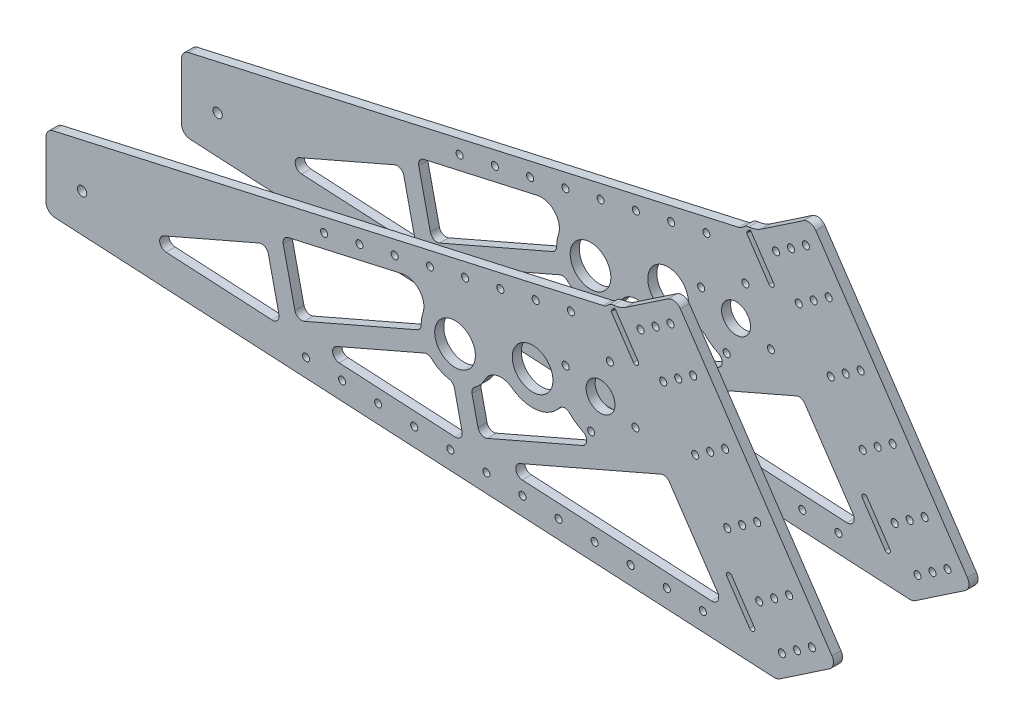
SolidWorks part; units mm, degrees
other "Markup1"
sketch "Sketch2"
sketch "Sketch9" plane through (0, 0, 0) normal (0, 0, 1) x (1, 0, 0)
sketch "Sketch12" plane through (116.0373, 167.646, 63.5) normal (0, 0, 1) x (1, 0, 0)
sketch "Sketch13" plane through (116.0373, 167.646, 63.5) normal (0, 0, 1) x (1, 0, 0)
sketch "Sketch14" plane through (116.0373, 167.646, 63.5) normal (0, 0, 1) x (1, 0, 0)
sketch "Sketch16" plane through (116.0373, 167.646, 63.5) normal (0, 0, 1) x (1, 0, 0)
sketch "Sketch17" plane through (116.0373, 167.8557, 63.5) normal (0, 0, 1) x (1, 0, 0)
sketch "Sketch18" plane through (116.0373, 167.7906, 57.15) normal (0, 0, 1) x (1, 0, 0)
sketch "Sketch19" plane through (84.5137, 127.089, 57.15) normal (0, 0, 1) x (1, 0, 0)
sketch "Sketch21" plane through (128.7373, 167.7931, 57.15) normal (0, 0, 1) x (1, 0, 0)
sketch "Sketch22" plane through (128.7373, 167.7931, 57.15) normal (0, 0, 1) x (1, 0, 0)
sketch "Sketch23" plane through (128.7373, 167.7931, 57.15) normal (0, 0, 1) x (1, 0, 0)
material "6061-T6 (SS)"
ref_plane "Front Plane" through (0, 0, 0) normal (0, 0, 1) x (1, 0, 0)
ref_plane "Top Plane" through (0, 0, 0) normal (0, 1, 0) x (1, 0, 0)
ref_plane "Right Plane" through (0, 0, 0) normal (1, 0, 0) x (0, 0, -1)
sketch "Grid" plane through (0, 0, 0) normal (0, 0, 1) x (1, 0, 0)
  line L0 (-23.2766, 0) -> (153.3593, 0) construction
  line L1 (0, 0) -> (0, 151.4205) construction
  line L6 (-1009.65, 1168.4) -> (-1009.65, 0) construction
  line L15 (-361.95, 520.7) -> (-803.275, 520.7)
  line L16 (-361.95, 520.7) -> (-361.95, 0)
  line L17 (-361.95, 0) -> (-803.275, 0)
  line L18 (-803.275, 520.7) -> (-803.275, 0)
  line L19 (-803.275, 0) -> (-1244.6, 0)
  line L20 (-803.275, 0) -> (-803.275, 825.5)
  line L21 (-803.275, 825.5) -> (-1244.6, 825.5)
  line L22 (-1244.6, 0) -> (-1244.6, 825.5)
  line L23 (-1030.732, 0) -> (-988.568, 0)
  line L24 (-1030.732, 0) -> (-1030.732, 1168.4)
  line L25 (-1030.732, 1168.4) -> (-988.568, 1168.4)
  line L26 (-988.568, 0) -> (-988.568, 1168.4)
  line L27 (-598.932, 0) -> (-556.768, 0)
  line L28 (-598.932, 0) -> (-598.932, 863.6)
  line L29 (-598.932, 863.6) -> (-556.768, 863.6)
  line L30 (-556.768, 0) -> (-556.768, 863.6)
  line L31 (-577.85, 863.6) -> (-577.85, 0) construction
  line L32 (-361.95, 520.7) -> (-361.95, 596.9) construction
  line L33 (-803.275, 825.5) -> (-803.275, 901.7) construction
  line L34 (-370.0766, 0) -> (-263.7141, 304.8)
  line L35 (-263.7141, 304.8) -> (-157.3516, 0)
  line L36 (-157.3516, 0) -> (-370.0766, 0)
  circle A0 centre (-100.3958, 159.9664) radius 120.65
  dimension "D3" = 241.3
  dimension "D2" = 76.2
  dimension "D4" = 304.8
  dimension "D5" = 212.725
  dimension "D7" = 42.164
  dimension "D8" = 520.7
  dimension "D9" = 304.8
  dimension "D10" = 1168.4
  dimension "D11" = 863.6
  dimension "D12" = 361.95
  dimension "D13" = 577.85
  dimension "D14" = 803.275
  dimension "D15" = 1009.65
sketch "ChassisXY" plane through (0, 0, 0) normal (0, 0, 1) x (1, 0, 0)
  line L0 (755.65, 93.726) -> (95.25, 93.726)
  line L1 (755.65, 93.726) -> (755.65, 42.926)
  line L2 (755.65, 42.926) -> (95.25, 42.926)
  line L3 (95.25, 93.726) -> (95.25, 42.926)
  line L15 (736.7108, 119.126) -> (675.4349, 119.126)
  line L16 (787.4, 42.926) -> (768.35, 42.926)
  line L19 (63.5, 169.926) -> (82.55, 169.926)
  line L20 (736.7108, 119.126) -> (694.5957, 90.719) construction
  line L21 (736.7108, 119.126) -> (717.55, 147.533) construction
  line L22 (694.5957, 90.719) -> (675.4349, 119.126) construction
  line L23 (717.55, 147.533) -> (675.4349, 119.126) construction
  line L27 (63.5, 169.926) -> (63.5, 42.926)
  line L31 (88.9, 42.926) -> (88.9, 1979.9925) construction
  line L32 (62.806, 1979.9925) -> (762, 1979.9925) construction
  line L33 (63.5, 42.926) -> (82.55, 42.926)
  line L36 (88.9, 1320.8) -> (762, 1320.8) construction
  line L37 (88.9, 988.6997) -> (131.0151, 1017.1067) construction
  line L45 (63.5, 42.926) -> (31.75, 42.926)
  line L46 (717.55, 147.533) -> (675.4349, 119.126) construction
  line L47 (717.55, 147.533) -> (-518.4596, 1979.9925) construction
  line L48 (675.4349, 119.126) -> (-560.5747, 1951.5855) construction
  line L49 (-518.4596, 1979.9925) -> (-560.5747, 1951.5855) construction
  line L50 (63.5, 42.926) -> (63.5, 169.926)
  line L51 (0, 74.676) -> (0, 138.176)
  line L52 (31.75, 169.926) -> (63.5, 169.926)
  line L54 (425.45, 93.726) -> (425.45, 42.926) construction
  line L55 (762, 42.926) -> (762, 1979.9925) construction
  line L56 (819.15, 169.926) -> (787.4, 169.926)
  line L57 (850.9, 74.676) -> (850.9, 138.176)
  line L58 (787.4, 42.926) -> (787.4, 169.926)
  line L59 (787.4, 42.926) -> (819.15, 42.926)
  line L60 (82.55, 169.926) -> (82.55, 42.926)
  line L61 (768.35, 169.926) -> (768.35, 42.926)
  line L62 (787.4, 169.926) -> (768.35, 169.926)
  line L63 (787.4, 169.926) -> (787.4, 42.926)
  line L64 (0, 0) -> (0, 200151.4205) construction
  line L65 (-200023.2766, 0) -> (200153.3593, 0) construction
  line L66 (95.25, 152.4) -> (755.65, 152.4) construction
  arc A5 (31.75, 169.926) -> (0, 138.176) centre (31.75, 138.176) ccw
  arc A6 (0, 74.676) -> (31.75, 42.926) centre (31.75, 74.676) ccw
  circle A7 centre (31.75, 74.676) radius 31.75 construction
  circle A8 centre (31.75, 138.176) radius 31.75 construction
  circle A9 centre (819.15, 138.176) radius 31.75 construction
  circle A10 centre (819.15, 74.676) radius 31.75 construction
  arc A11 (850.9, 74.676) -> (819.15, 42.926) centre (819.15, 74.676) cw
  arc A12 (819.15, 169.926) -> (850.9, 138.176) centre (819.15, 138.176) cw
  dimension "D3" = 63.5
  dimension "D1" = 50.8
  dimension "D2" = 56
  dimension "D4" = 38.1
  dimension "D5" = 50.8
  dimension "D6" = 12.7
  dimension "D7" = 19.05
  dimension "D8" = 42.926
  dimension "D9" = 109.474
  dimension "D10" = 25.4
  dimension "D12" = 660.4
  dimension "D13" = 6.35
ref_plane "Plane1" through (561.5696, 378.7835, 0) normal (0.829, 0.5592, 0) x (-0.5592, 0.829, 0)
sketch "carriage geo" plane through (0, 0, 0) normal (0, 0, 1) x (1, 0, 0)
  line L1 (116.0373, 195.326) -> (624.0373, 195.326)
  line L2 (116.0373, 195.326) -> (116.0373, 246.126)
  line L3 (116.0373, 246.126) -> (624.0373, 246.126)
  line L4 (624.0373, 195.326) -> (624.0373, 246.126)
  line L6 (624.0373, 195.326) -> (700.6322, 195.326) construction
  line L17 (717.55, 147.533) -> (-518.4596, 1979.9925) construction
  line L24 (624.0373, 246.126) -> (666.3671, 246.126) construction
  line L33 (666.3671, 246.126) -> (700.6322, 195.326) construction
  line L35 (675.4349, 119.126) -> (-560.5747, 1951.5855) construction
  line L64 (755.65, 93.726) -> (95.25, 93.726) construction
  circle A0 centre (154.1373, 220.726) radius 14.2875
  circle A58 centre (256.8816, 507.741) radius 25.4
  line B0 (120.4355, 364.2548) -> (144.4436, 355.656) construction
  line B1 (345.3934, 565.2279) -> (248.3868, 535.0242)
  line B2 (339.9907, 375.4447) -> (343.9447, 374.0285) construction
  line B3 (348.2442, 386.0326) -> (300.3235, 403.196) construction
  line B4 (308.577, 413.7839) -> (348.5895, 399.4529)
  line B5 (107.1432, 327.1426) -> (206.8255, 291.4401)
  line B6 (112.3162, 360.4178) -> (103.3062, 335.2619)
  line B7 (352.5436, 398.0367) -> (348.5895, 399.4529) construction
  line B8 (366.599, 439.1494) -> (341.413, 442.4393) construction
  line B9 (353.8882, 537.9448) -> (341.413, 442.4393) construction
  line B10 (343.9447, 374.0285) -> (352.5436, 398.0367)
  line B11 (348.5895, 399.4529) -> (308.577, 413.7839)
  line B12 (304.6229, 415.2001) -> (296.0241, 391.1919)
  line B13 (299.9781, 389.7757) -> (339.9907, 375.4447)
  line B14 (140.4752, 344.576) -> (141.8914, 348.5301) construction
  line B15 (129.3385, 325.9381) -> (133.2925, 324.5219) construction
  line B16 (110.7006, 337.0748) -> (109.2844, 333.1207) construction
  line B17 (121.8372, 355.7127) -> (117.8832, 357.1289) construction
  line B18 (117.8832, 357.1289) -> (110.7006, 337.0748)
  line B19 (109.2844, 333.1207) -> (129.3385, 325.9381)
  line B20 (141.8914, 348.5301) -> (121.8372, 355.7127)
  line B21 (133.2925, 324.5219) -> (140.4752, 344.576)
  line B22 (296.0241, 391.1919) -> (299.9781, 389.7757) construction
  line B23 (308.577, 413.7839) -> (304.6229, 415.2001) construction
  arc B24 (248.3868, 535.0242) -> (233.4586, 491.3735) centre (256.8816, 507.741) ccw
  circle B25 centre (256.8816, 507.741) radius 3.1877
  circle B26 centre (353.8882, 537.9448) radius 3.1877
  arc B27 (107.1432, 327.1426) -> (103.3062, 335.2619) centre (109.2844, 333.1207) cw
  circle B28 centre (341.413, 442.4393) radius 30 construction
  arc B29 (121.2422, 363.9009) -> (112.3162, 360.4178) centre (118.2943, 358.2767) ccw
  arc B30 (233.4586, 491.3735) -> (121.2422, 363.9009) centre (161.817, 441.3116) cw
  circle B31 centre (341.413, 442.4393) radius 25.4 construction
  circle B32 centre (366.599, 439.1494) radius 2.4892
  circle B33 centre (338.1231, 417.2533) radius 2.4892
  circle B34 centre (316.2269, 445.7292) radius 2.4892
  circle B35 centre (344.7029, 467.6254) radius 2.4892
  circle B36 centre (341.413, 442.4393) radius 10.16
  circle B37 centre (147.3899, 326.2177) radius 2.4892
  arc B38 (376.4624, 520.4251) -> (367.6342, 457.9958) centre (426.6271, 481.4924) ccw
  arc B39 (367.6342, 457.9958) -> (206.8255, 291.4401) centre (249.6484, 411.0026) cw
  arc B40 (133.2925, 324.5219) -> (129.3385, 325.9381) centre (131.3155, 325.23) cw
  arc B41 (343.9447, 374.0285) -> (339.9907, 375.4447) centre (341.9677, 374.7366) cw
  arc B42 (296.0241, 391.1919) -> (299.9781, 389.7757) centre (298.0011, 390.4838) ccw
  arc B43 (352.5436, 398.0367) -> (348.5895, 399.4529) centre (350.5666, 398.7448) ccw
  arc B44 (304.6229, 415.2001) -> (308.577, 413.7839) centre (306.5999, 414.492) cw
  arc B45 (109.2844, 333.1207) -> (110.7006, 337.0748) centre (109.9925, 335.0977) cw
  arc B46 (117.8832, 357.1289) -> (121.8372, 355.7127) centre (119.8602, 356.4208) cw
  arc B47 (141.8914, 348.5301) -> (140.4752, 344.576) centre (141.1833, 346.553) cw
  circle B48 centre (353.8882, 537.9448) radius 28.575
  line B49 (343.9447, 374.0285) -> (296.1197, 391.1577)
  line B50 (343.9447, 374.0285) -> (318.251, 302.291)
  line B51 (296.1197, 391.1577) -> (270.426, 319.4201)
  line B52 (318.251, 302.291) -> (270.426, 319.4201) construction
  line B53 (141.8571, 348.4344) -> (133.2925, 324.5219) construction
  line B54 (165.7696, 339.8698) -> (237.5071, 314.1761)
  line B55 (157.205, 315.9573) -> (228.9426, 290.2636)
  line B56 (237.5071, 314.1761) -> (228.9426, 290.2636) construction
  line B57 (161.4873, 327.9136) -> (233.2249, 302.2198) construction
  line B58 (165.7696, 339.8698) -> (157.205, 315.9573)
  line B59 (133.2925, 324.5219) -> (157.205, 315.9573) construction
  line B60 (141.8571, 348.4344) -> (165.7696, 339.8698) construction
  line B61 (308.4359, 312.5514) -> (331.9885, 378.3108) construction
  line B62 (320.0322, 382.5931) -> (294.3385, 310.8556) construction
  arc B63 (155.075, 274.6929) -> (165.7608, 168.0174) centre (154.1373, 220.726) ccw
  circle B64 centre (176.5553, 212.6967) radius 2.4892
  circle B65 centre (158.3928, 197.2968) radius 2.4892
  circle B66 centre (135.9748, 205.3261) radius 2.4892
  circle B67 centre (131.7194, 228.7553) radius 2.4892
  circle B68 centre (149.8819, 244.1552) radius 2.4892
  circle B69 centre (172.2999, 236.1259) radius 2.4892
  circle B70 centre (154.1373, 220.726) radius 23.8125 construction
  circle B71 centre (308.4359, 312.5514) radius 2.4892
  arc B72 (165.7608, 168.0174) -> (155.075, 274.6929) centre (154.1373, 220.726) ccw construction
  circle B73 centre (227.2467, 304.361) radius 2.4892
  circle B74 centre (284.5234, 321.116) radius 2.4892
  arc B75 (290.7123, 376.06) -> (193.2811, 330.0162) centre (218.9748, 401.7538) cw
  arc B76 (318.251, 302.291) -> (165.7608, 168.0174) centre (120.5341, 373.1059) cw
  circle B77 centre (312.7182, 324.5077) radius 2.4892
  circle B78 centre (288.8057, 333.0722) radius 2.4892
  circle B79 centre (317.0005, 336.4639) radius 2.4892
  circle B80 centre (293.088, 345.0285) radius 2.4892
  circle B81 centre (321.2828, 348.4202) radius 2.4892
  circle B82 centre (297.3703, 356.9847) radius 2.4892
  circle B83 centre (325.5651, 360.3764) radius 2.4892
  circle B84 centre (301.6526, 368.941) radius 2.4892
  circle B85 centre (329.8473, 372.3327) radius 2.4892
  circle B86 centre (305.9348, 380.8972) radius 2.4892
  arc B87 (162.2796, 314.1398) -> (155.075, 274.6929) centre (155.4279, 295.0098) cw
  circle B88 centre (215.2905, 308.6433) radius 2.4892
  circle B89 centre (203.3342, 312.9256) radius 2.4892
  circle B90 centre (191.378, 317.2079) radius 2.4892
  circle B91 centre (179.4217, 321.4901) radius 2.4892
  circle B92 centre (167.4655, 325.7724) radius 2.4892
  dimension "D2" = 28.575
  dimension "D3" = 25.4
  dimension "D4" = 38.1
  dimension "D8" = 101.6
  dimension "D5" = 50.8
  dimension "D1" = 50.8
  dimension "D6" = 12.7
  dimension "D7" = 508
sketch_block_instance "Block25-1"
sketch_block "Block25"
sketch_block_instance "Block26-1"
sketch_block "Block26"
sketch "carrriageyz" plane through (561.5696, 378.7835, 0) normal (0.829, 0.5592, 0) x (-0.5592, 0.829, 0)
  line L0 (-313.2035, 63.5) -> (769.957, 63.5) construction
  line L1 (769.957, -63.5) -> (-313.2035, -63.5) construction
  line L2 (-262.4035, 63.5) -> (-262.4035, -63.5) construction
  line L4 (-313.2035, 63.5) -> (-313.2035, -63.5) construction
  line L5 (-313.2035, 0) -> (-278.9385, 0) construction
  line L6 (769.957, 63.5) -> (769.957, -63.5) construction
  line L7 (-249.7114, 50.8) -> (-249.7114, 44.45)
  line L8 (-249.7114, 50.8) -> (-97.3114, 50.8)
  line L9 (-249.7114, 44.45) -> (-97.3114, 44.45)
  line L10 (-97.3114, 50.8) -> (-97.3114, 44.45)
  line L11 (55, 0) -> (-55, 0) construction
  line L12 (-97.3114, -50.8) -> (-97.3114, -44.45)
  line L13 (-249.7114, -44.45) -> (-97.3114, -44.45)
  line L14 (-249.7114, -50.8) -> (-97.3114, -50.8)
  line L15 (-249.7114, -50.8) -> (-249.7114, -44.45)
  line L16 (-218.5469, 31.75) -> (-148.6639, 31.75)
  line L17 (-174.4547, 50.8) -> (-206.8488, 50.8)
  line L19 (-221.2897, -50.8) -> (-160.0138, -50.8)
  line L21 (-219.5489, -50.8) -> (-127.4739, -50.8)
  line L22 (-219.5489, 57.15) -> (-127.4739, 57.15)
  line L23 (-219.5489, 57.15) -> (-219.5489, 50.8)
  line L24 (-219.5489, 50.8) -> (-127.4739, 50.8)
  line L25 (-127.4739, 57.15) -> (-127.4739, 50.8)
  line L26 (-127.4739, -57.15) -> (-127.4739, -50.8)
  line L27 (-219.5489, -57.15) -> (-127.4739, -57.15)
  line L28 (-219.5489, -57.15) -> (-219.5489, -50.8)
  line L29 (-218.5469, 31.75) -> (-218.5469, -31.75)
  line L30 (-218.5469, -31.75) -> (-148.6639, -31.75)
  line L31 (-148.6639, 31.75) -> (-148.6639, -31.75)
  line L33 (-97.3114, -62.7634) -> (-125.8864, -62.7634)
  line L34 (-97.3114, 50.8) -> (-125.8864, 50.8)
  line L35 (-97.3114, 50.8) -> (-97.3114, 62.7634)
  line L36 (-97.3114, 62.7634) -> (-125.8864, 62.7634)
  line L37 (-125.8864, 50.8) -> (-125.8864, 62.7634)
  line L38 (-249.7114, 50.8) -> (-221.1364, 50.8)
  line L39 (-249.7114, 50.8) -> (-249.7114, 62.7634)
  line L40 (-249.7114, 62.7634) -> (-221.1364, 62.7634)
  line L41 (-221.1364, 50.8) -> (-221.1364, 62.7634)
  line L42 (-125.8864, -50.8) -> (-125.8864, -62.7634)
  line L43 (-97.3114, -50.8) -> (-125.8864, -50.8)
  line L44 (-97.3114, -50.8) -> (-97.3114, -62.7634)
  line L45 (-249.7114, -62.7634) -> (-221.1364, -62.7634)
  line L46 (-221.1364, -50.8) -> (-221.1364, -62.7634)
  line L47 (-249.7114, -50.8) -> (-221.1364, -50.8)
  line L48 (-249.7114, -50.8) -> (-249.7114, -62.7634)
  line L49 (-111.5989, 62.7634) -> (-111.5989, -62.7634) construction
  line L50 (-235.4239, 62.7634) -> (-235.4239, -62.7634) construction
  point P4 (-313.2035, 0)
  point P31 (-148.6639, 0)
  point P41 (-190.6518, 50.8)
  point P53 (-111.5989, 0)
  dimension "D1" = 127
  dimension "D2" = 12.7
  dimension "D3" = 6.35
  dimension "D4" = 63.5
  dimension "D5" = 6.35
  dimension "D6" = 152.4
  dimension "D7" = 28.575
  dimension "D8" = 11.9634
  dimension "D9" = 50.8
  dimension "D10" = 1.5875
  dimension "D11" = 1.5875
ref_plane "bearing block interface plane" through (0, 0, 50.8) normal (0, 0, 1) x (1, 0, 0)
sketch "bearing block interface plate" plane through (0, 0, 50.8) normal (0, 0, 1) x (1, 0, 0)
  line L0 (529.0514, 336.1484) -> (571.1665, 364.5554)
  line L1 (529.0514, 336.1484) -> (642.6794, 167.688)
  line L2 (571.1665, 364.5554) -> (684.7945, 196.095)
  line L3 (642.6794, 167.688) -> (684.7945, 196.095)
  line L4 (675.4349, 119.126) -> (-560.5747, 1951.5855) construction
  line L5 (717.55, 147.533) -> (-518.4596, 1979.9925) construction
  line L6 (635.5777, 178.2167) -> (677.6928, 206.6237) construction
  line L7 (585.8654, 251.9182) -> (627.9805, 280.3252) construction
  line L10 (545.0304, 312.4586) -> (587.1455, 340.8656) construction
  line L12 (528.3092, 320.3288) -> (546.682, 332.7214) construction
  line L15 (606.2073, 289.894) -> (628.6962, 256.5529) construction
  line L16 (522.4272, 322.7212) -> (526.7202, 333.2764) construction
  line L17 (529.0514, 336.1484) -> (536.1532, 325.6196) construction
  line L18 (527.0768, 314.0996) -> (540.247, 311.4938) construction
  line L21 (577.876, 263.7631) -> (619.9911, 292.1701) construction
  line L22 (626.7005, 191.3777) -> (668.8156, 219.7847) construction
  line L23 (611.7695, 190.2657) -> (623.1643, 190.2921) construction
  line L24 (610.7216, 215.0675) -> (652.8367, 243.4745) construction
  line L25 (605.5175, 197.8065) -> (608.0351, 210.9939) construction
  line L26 (611.7548, 196.6157) -> (630.1275, 209.0082) construction
  circle A0 centre (646.1065, 185.3185) radius 2.4892
  circle A1 centre (656.6352, 192.4202) radius 2.4892
  circle A2 centre (667.164, 199.522) radius 2.4892
  circle A3 centre (567.7395, 346.9249) radius 2.4892
  circle A4 centre (557.2107, 339.8231) radius 2.4892
  circle A5 centre (546.682, 332.7214) radius 2.4892
  arc A7 (522.4272, 322.7212) -> (527.0768, 314.0996) centre (528.3092, 320.3288) ccw construction
  circle A12 centre (562.6609, 309.0316) radius 2.4892
  circle A13 centre (573.1897, 316.1334) radius 2.4892
  circle A14 centre (583.7185, 323.2351) radius 2.4892
  circle A15 centre (606.2073, 289.894) radius 2.4892
  circle A16 centre (595.6786, 282.7922) radius 2.4892
  circle A17 centre (585.1498, 275.6905) radius 2.4892
  circle A18 centre (628.6962, 256.5529) radius 2.4892
  circle A19 centre (618.1674, 249.4511) radius 2.4892
  circle A20 centre (607.6387, 242.3494) radius 2.4892
  circle A21 centre (651.1851, 223.2117) radius 2.4892
  circle A22 centre (640.6563, 216.11) radius 2.4892
  circle A23 centre (630.1275, 209.0082) radius 2.4892
  arc A24 (526.7202, 333.2764) -> (529.0514, 336.1484) centre (532.6023, 330.884) cw construction
  arc A25 (540.247, 311.4938) -> (545.0304, 312.4586) centre (541.4795, 317.723) ccw construction
  arc A29 (623.1643, 190.2921) -> (626.7005, 191.3777) centre (623.1496, 196.6421) ccw construction
  arc A30 (611.7695, 190.2657) -> (605.5175, 197.8065) centre (611.7548, 196.6157) cw construction
  arc A31 (608.0351, 210.9939) -> (610.7216, 215.0675) centre (614.2724, 209.8031) cw construction
  point P28 (617.4518, 273.2234)
  dimension "D3" = 4.9784
  dimension "D8" = 12.7
  dimension "D10" = 2
  dimension "D13" = 6.35
  dimension "D1" = 12.7
  dimension "D2" = 12.7
  dimension "D4" = 12.7
  dimension "D5" = 28.575
  dimension "D6" = 203.2
  dimension "D7" = 33.3375
  dimension "D9" = 9.4615
  dimension "D11" = 4
  dimension "D12" = 12.7
extrude "Boss-Extrude1" add sketch "bearing block interface plate" against normal blind 6.35
fillet "Fillet2" radius 6.35 4 edges at (642.6794, 167.688, 47.625) (571.1665, 364.5554, 47.625) (529.0514, 336.1484, 47.625) (684.7945, 196.095, 47.625)
ref_plane "carriage support plane" through (0, 0, 50.8) normal (0, 0, 1) x (1, 0, 0)
sketch "plate+gb" plane through (0, 0, 50.8) normal (0, 0, 1) x (1, 0, 0)
  line L1 (717.55, 147.533) -> (-518.4596, 1979.9925) construction
  line L3 (116.0373, 195.326) -> (624.0373, 195.326) construction
  line L4 (128.7373, 195.326) -> (642.6794, 167.688)
  line L8 (532.6023, 330.884) -> (639.1286, 172.9523) construction
  line L10 (116.0373, 246.126) -> (624.0373, 246.126) construction
  line L11 (128.7373, 246.126) -> (128.7373, 195.326)
  line L12 (116.0373, 195.326) -> (116.0373, 246.126) construction
  line L13 (571.1665, 364.5554) -> (529.0514, 336.1484)
  line L17 (527.3934, 335.03) -> (543.3723, 311.3403) construction
  line L18 (529.0514, 336.1484) -> (545.0304, 312.4586)
  line L19 (416.2866, 258.7212) -> (154.1373, 220.726) construction
  line L20 (416.2683, 274.9957) -> (154.0767, 274.701) construction
  line L21 (420.8895, 243.1112) -> (169.4032, 168.9548) construction
  line L22 (518.57, 277.876) -> (525.144, 302.4105) construction
  line L24 (527.3966, 335.7763) -> (128.7373, 246.126)
  line L26 (256.3165, 274.8159) -> (527.3966, 335.7763) construction
  line L27 (528.1615, 331.9493) -> (527.3934, 335.03) construction
  line L30 (525.7353, 333.9116) -> (541.7142, 310.2219)
  line L31 (529.0514, 336.1484) -> (642.6794, 167.688) construction
  line L38 (642.6794, 167.688) -> (684.7945, 196.095) construction
  line L39 (642.6794, 167.688) -> (684.7945, 196.095)
  line L40 (545.0304, 312.4586) -> (587.1455, 340.8656) construction
  line L43 (609.0635, 213.9491) -> (625.0424, 190.2593) construction
  line L44 (610.7216, 215.0675) -> (626.7005, 191.3777)
  line L45 (607.4054, 212.8307) -> (623.3843, 189.1409)
  line L59 (684.7945, 196.095) -> (571.1665, 364.5554)
  circle A0 centre (470.8051, 270.9813) radius 14.2875
  circle A1 centre (416.2866, 258.7212) radius 14.2875
  arc A2 (155.075, 274.6929) -> (165.7608, 168.0174) centre (154.1373, 220.726) ccw construction
  arc A4 (165.7608, 168.0174) -> (155.075, 274.6929) centre (154.1373, 220.726) ccw construction
  circle A5 centre (518.57, 277.876) radius 10.16
  circle A12 centre (518.57, 277.876) radius 25.4 construction
  circle A13 centre (518.57, 277.876) radius 7.62 construction
  circle A14 centre (470.8051, 270.9813) radius 40.64 construction
  circle A15 centre (470.8051, 270.9813) radius 15.24 construction
  circle A16 centre (416.2866, 258.7212) radius 40.64 construction
  circle A17 centre (416.2866, 258.7212) radius 16.2745 construction
  circle A18 centre (525.144, 302.4105) radius 2.4892
  circle A19 centre (543.1045, 271.302) radius 2.4892
  circle A20 centre (511.996, 253.3415) radius 2.4892
  circle A21 centre (494.0355, 284.45) radius 2.4892
  arc A22 (529.0514, 336.1484) -> (525.7353, 333.9116) centre (527.3934, 335.03) ccw
  arc A23 (541.7142, 310.2219) -> (545.0304, 312.4586) centre (543.3723, 311.3403) ccw
  arc A24 (610.7216, 215.0675) -> (607.4054, 212.8307) centre (609.0635, 213.9491) ccw
  circle A25 centre (607.6387, 242.3494) radius 2.4892 construction
  circle A26 centre (618.1674, 249.4511) radius 2.4892 construction
  circle A27 centre (628.6962, 256.5529) radius 2.4892 construction
  circle A28 centre (606.2073, 289.894) radius 2.4892 construction
  circle A29 centre (595.6786, 282.7922) radius 2.4892 construction
  circle A30 centre (585.1498, 275.6905) radius 2.4892 construction
  circle A31 centre (562.6609, 309.0316) radius 2.4892 construction
  circle A32 centre (573.1897, 316.1334) radius 2.4892 construction
  circle A33 centre (583.7185, 323.2351) radius 2.4892 construction
  circle A35 centre (518.57, 277.876) radius 30 construction
  circle A41 centre (607.6387, 242.3494) radius 2.4892
  circle A42 centre (618.1674, 249.4511) radius 2.4892
  circle A43 centre (628.6962, 256.5529) radius 2.4892
  circle A44 centre (606.2073, 289.894) radius 2.4892
  circle A45 centre (595.6786, 282.7922) radius 2.4892
  circle A46 centre (585.1498, 275.6905) radius 2.4892
  circle A47 centre (562.6609, 309.0316) radius 2.4892
  circle A48 centre (573.1897, 316.1334) radius 2.4892
  circle A49 centre (583.7185, 323.2351) radius 2.4892
  arc A59 (623.3843, 189.1409) -> (626.7005, 191.3777) centre (625.0424, 190.2593) ccw
  circle A63 centre (567.7395, 346.9249) radius 2.4892 construction
  circle A68 centre (557.2107, 339.8231) radius 2.4892 construction
  circle A74 centre (546.682, 332.7214) radius 2.4892 construction
  circle A75 centre (651.1851, 223.2117) radius 2.4892 construction
  circle A77 centre (640.6563, 216.11) radius 2.4892 construction
  circle A78 centre (630.1275, 209.0082) radius 2.4892 construction
  circle A79 centre (567.7395, 346.9249) radius 2.4892
  circle A80 centre (557.2107, 339.8231) radius 2.4892
  circle A81 centre (546.682, 332.7214) radius 2.4892
  circle A82 centre (651.1851, 223.2117) radius 2.4892
  circle A83 centre (640.6563, 216.11) radius 2.4892
  circle A84 centre (630.1275, 209.0082) radius 2.4892
  circle A85 centre (646.1065, 185.3185) radius 2.4892 construction
  circle A86 centre (656.6352, 192.4202) radius 2.4892 construction
  circle A87 centre (667.164, 199.522) radius 2.4892 construction
  arc A88 (530.9003, 337.3954) -> (522.7356, 334.7281) centre (528.1615, 331.9493) ccw
  arc A89 (527.61, 338.0203) -> (536.5393, 341.1991) centre (525.8867, 356.9922) ccw
  arc A90 (528.6076, 336.8064) -> (525.985, 333.5754) centre (532.6023, 330.884) ccw
  circle A91 centre (646.1065, 185.3185) radius 2.4892
  circle A93 centre (656.6352, 192.4202) radius 2.4892
  circle A94 centre (667.164, 199.522) radius 2.4892
  arc A95 (530.3158, 337.652) -> (525.9764, 333.5542) centre (532.6023, 330.884) ccw
  point P10 (535.3828, 323.1851)
  point P47 (617.053, 202.1042)
  point P64 (518.57, 277.876)
  dimension "D2" = 50.8
  dimension "D15" = 28.575
  dimension "D16" = 20.32
  dimension "D18" = 4.9784
  dimension "D14" = 6.096
  dimension "D24" = 19.05
  dimension "D19" = 15
  dimension "D20" = 31.75
  dimension "D11" = 4
  dimension "D8" = 41.275
  dimension "D9" = 50.8
  dimension "D10" = 50.8
  dimension "D12" = 12.7
  dimension "D21" = 20
  dimension "D23" = 3.175
  dimension "D13" = 0.7937
  dimension "D17" = 4
extrude "Boss-Extrude2" add sketch "plate+gb" against normal blind 6.35
fillet "Fillet1" radius 6.35 6 edges at (128.7373, 195.326, 47.625) (128.7373, 246.126, 47.625) (571.1665, 364.5554, 47.625) (642.6794, 167.688, 47.625) (684.7945, 196.095, 47.625) (522.7356, 334.7281, 47.625)
sketch "tube" plane through (0, 0, 50.8) normal (0, 0, 1) x (1, 0, 0)
  line L7 (522.5096, 324.9144) -> (135.7839, 237.9478)
  line L11 (135.4283, 207.6845) -> (641.235, 180.484)
  line L12 (135.4283, 207.6845) -> (641.235, 180.484) construction
  line L13 (522.5096, 324.9144) -> (135.7839, 237.9478) construction
  circle A48 centre (497.7285, 319.3416) radius 2.4892
  circle A49 centre (472.9474, 313.7689) radius 2.4892
  circle A50 centre (448.1662, 308.1961) radius 2.4892
  circle A51 centre (423.3851, 302.6233) radius 2.4892
  circle A52 centre (398.604, 297.0506) radius 2.4892
  circle A53 centre (373.8229, 291.4778) radius 2.4892
  circle A54 centre (590.5083, 183.2119) radius 2.4892
  circle A55 centre (565.1449, 184.5758) radius 2.4892
  circle A56 centre (539.7816, 185.9398) radius 2.4892
  circle A57 centre (514.4182, 187.3038) radius 2.4892
  circle A58 centre (489.0549, 188.6677) radius 2.4892
  circle A59 centre (463.6915, 190.0317) radius 2.4892
  circle A60 centre (438.3282, 191.3956) radius 2.4892
  circle A61 centre (412.9648, 192.7596) radius 2.4892
  circle A62 centre (387.6015, 194.1235) radius 2.4892
  circle A63 centre (362.2381, 195.4875) radius 2.4892
  circle A64 centre (336.8748, 196.8514) radius 2.4892
  circle A65 centre (311.5114, 198.2154) radius 2.4892
  circle A70 centre (349.0417, 285.905) radius 2.4892
  circle A71 centre (324.2606, 280.3323) radius 2.4892
  circle A74 centre (154.1373, 220.726) radius 3.2639
  dimension "D3" = 12.7
  dimension "D4" = 4.9784
  dimension "D5" = 50.8
  dimension "D15" = 25.4
  dimension "D2" = 6.5278
  dimension "D7" = 12
  dimension "D11" = 9.525
  dimension "D16" = 25.4
  dimension "D6" = 25.4
extrude "Cut-Extrude1" cut sketch "tube" against normal up to next
sketch "Sketch20" plane through (0, 0, 50.8) normal (0, 0, 1) x (1, 0, 0)
  line L0 (178.8573, 214.8878) -> (288.2885, 262.48) construction
  line L1 (288.2885, 262.48) -> (300.4616, 208.3484) construction
  line L2 (300.4616, 208.3484) -> (416.2866, 258.7212) construction
  line L3 (416.2866, 258.7212) -> (429.1709, 201.4268) construction
  line L4 (429.1709, 201.4268) -> (561.0825, 258.7959) construction
  line L5 (181.3898, 209.0647) -> (283.7782, 253.5939)
  line L6 (283.7782, 253.5939) -> (295.9513, 199.4623)
  line L7 (295.9513, 199.4623) -> (411.7763, 249.8352)
  line L8 (173.8491, 236.745) -> (522.9963, 315.261)
  line L9 (522.9963, 315.261) -> (606.1998, 191.9068)
  line L10 (606.1998, 191.9068) -> (178.8573, 214.8878)
  line L11 (134.7464, 195.0029) -> (640.553, 167.8023) construction
  line L12 (520.4198, 334.2073) -> (133.6942, 247.2407) construction
  line L13 (525.9764, 333.5542) -> (541.7142, 310.2219) construction
  line L14 (128.7373, 241.0454) -> (128.7373, 201.3437) construction
  line L15 (411.7763, 249.8352) -> (424.6606, 192.5407)
  line L16 (424.6606, 192.5407) -> (564.6938, 253.4419)
  line L17 (176.3248, 220.711) -> (292.7988, 271.3661)
  line L18 (292.7988, 271.3661) -> (304.9719, 217.2345)
  line L19 (304.9719, 217.2345) -> (420.7969, 267.6073)
  line L20 (420.7969, 267.6073) -> (433.6812, 210.3129)
  line L21 (433.6812, 210.3129) -> (558.55, 264.619)
  line L22 (424.6606, 192.5407) -> (563.6151, 252.9727) construction
  arc A0 (378.9306, 282.8636) -> (393.7412, 266.3854) centre (381.717, 270.473) cw
  arc A1 (492.8846, 262.0635) -> (548.723, 277.1196) centre (518.57, 277.876) ccw
  circle A2 centre (518.57, 277.876) radius 10.16 construction
  circle A3 centre (511.996, 253.3415) radius 4.7625 construction
  circle A4 centre (154.1373, 220.726) radius 14.2875 construction
  circle A8 centre (154.1373, 220.726) radius 25.4
  circle A9 centre (416.2866, 258.7212) radius 23.8125
  circle A10 centre (470.8051, 270.9813) radius 23.8125
  circle A12 centre (416.2866, 258.7212) radius 14.2875 construction
  arc A13 (430.701, 277.6754) -> (449.6639, 281.9398) centre (438.3887, 287.7843) ccw
  arc A14 (437.4277, 247.7628) -> (456.3907, 252.0272) centre (448.703, 241.9183) cw
  dimension "D4" = 9.525
  dimension "D5" = 12.7
  dimension "D6" = 9.525
  dimension "D1" = 22.225
  dimension "D2" = 19.05
  dimension "D3" = 12.7
  dimension "D7" = 6.35
  dimension "D8" = 6.35
extrude "Cut-Extrude2" cut sketch "Sketch20" against normal up to next contours L10 L6 L5 | A9 A0 L8 L18 L19 | A9 L7 L10 L15 | A14 A9 L20 L21 A1 A10 | L16 L10 L9
fillet "Fillet3" radius 4.7625 17 edges at (392.7081, 255.3914, 47.625) (304.9719, 217.2345, 47.625) (294.4838, 263.8732, 47.625) (492.8846, 262.0635, 47.625) (519.7296, 247.7358, 47.625) (433.6812, 210.3129, 47.625) (427.5171, 237.7234, 47.625) (564.6938, 253.4419, 47.625) (606.1998, 191.9068, 47.625) (443.3407, 200.6648, 47.625) (415.1266, 234.937, 47.625) (422.5827, 201.7811, 47.625) (314.6314, 207.5864, 47.625) (397.7731, 243.7451, 47.625) (283.7782, 253.5939, 47.625) (293.8733, 208.7027, 47.625) (193.0271, 214.1258, 47.625)
fillet "Fillet4" radius 0.635 2 edges at (528.4731, 336.7135, 47.625) (525.9764, 333.5542, 47.625)
mirror "Mirror1" about plane through (0, 0, 0) normal (0, 0, 1) of bodies 115 105 104 101
equation "\"D3@plate+gb\" = 12 / 20"
equation "\"D4@plate+gb\" = 64 / 20"
equation "\"D5@plate+gb\" = 24 / 20"
equation "\"D6@plate+gb\" = 64 / 20"
equation "\"D7@plate+gb\" = 0.25 /  ( sin ( 180 / 16 )  ) "
equation "\"D22@plate+gb\"=60mm"
